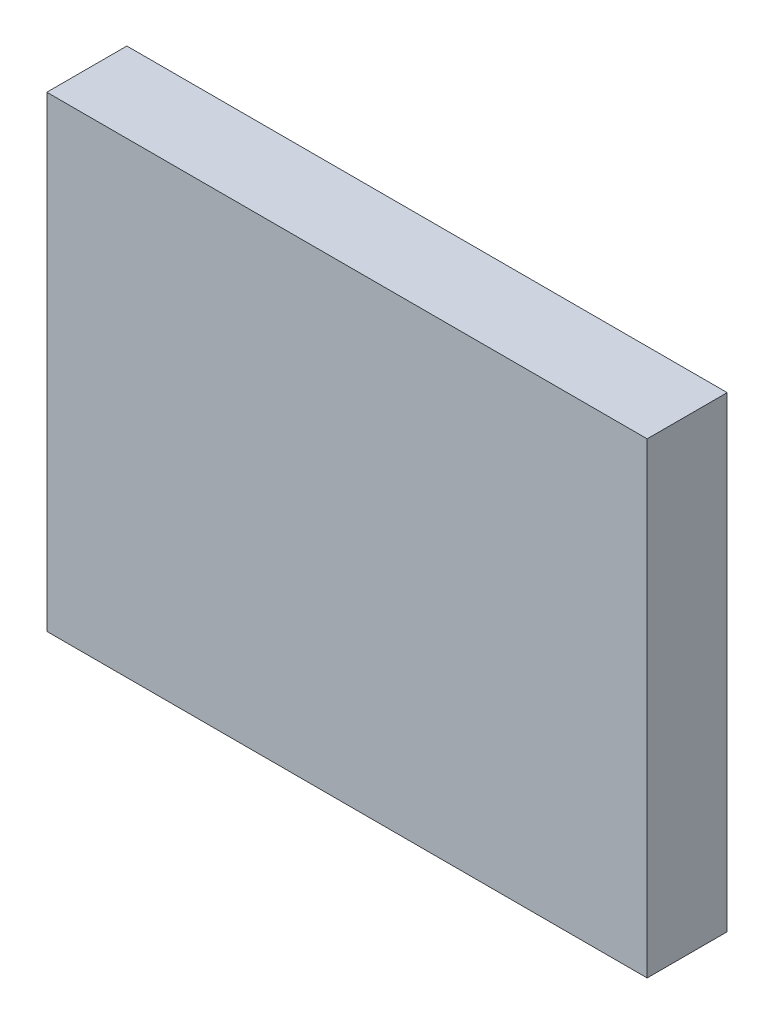
SolidWorks part; units mm, degrees
ref_plane "Front Plane" through (0, 0, 0) normal (0, 0, 1) x (1, 0, 0)
ref_plane "Top Plane" through (0, 0, 0) normal (0, 1, 0) x (1, 0, 0)
ref_plane "Right Plane" through (0, 0, 0) normal (1, 0, 0) x (0, 0, -1)
sketch "Sketch1" plane through (0, 0, 0) normal (0, 0, 1) x (1, 0, 0)
  line L0 (-4.5, 3.5) -> (-4.5, -3.5)
  line L1 (-4.5, -3.5) -> (4.5, -3.5)
  line L2 (4.5, -3.5) -> (4.5, 3.5)
  line L3 (4.5, 3.5) -> (-4.5, 3.5)
  dimension "D1" = 3.5
  dimension "D2" = 7
  dimension "D3" = 4.5
  dimension "D4" = 9
extrude "Boss-Extrude1" add sketch "Sketch1" along normal blind 1.2 contours L3 L0 L1 L2
